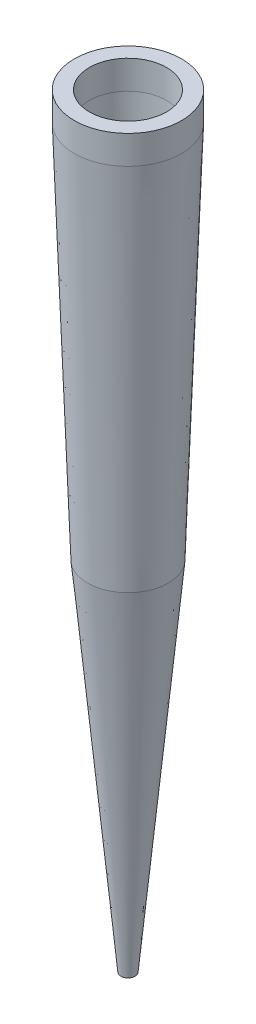
SolidWorks part; units mm, degrees
ref_plane "Ebene vorne" through (0, 0, 0) normal (0, 0, 1) x (1, 0, 0)
ref_plane "Ebene oben" through (0, 0, 0) normal (0, 1, 0) x (1, 0, 0)
ref_plane "Ebene rechts" through (0, 0, 0) normal (1, 0, 0) x (0, 0, -1)
sketch "Skizze1" plane through (0, 0, 0) normal (0, 0, 1) x (1, 0, 0)
  line L0 (0, 0) -> (0, -16.3942) construction
  line L1 (-2.7, 0) -> (-2.7, -2)
  line L2 (-2.7, -2) -> (-1.7746, -28.5)
  line L3 (-1.7746, -28.5) -> (-0.5, -53.5)
  line L5 (-0.5, -53.5) -> (-2.8246, -28.5)
  line L6 (-2.8246, -28.5) -> (-3.75, -2)
  line L7 (-3.75, -2) -> (-3.75, 0)
  line L8 (-3.75, 0) -> (-2.7, 0)
  dimension "D1" = 2.7
  dimension "D2" = 53.5
  dimension "D3" = 2
  dimension "D4" = 7.5
  dimension "D5" = 1
  dimension "D6" = 182
  dimension "D7" = 25
revolve "Rotation1" add sketch "Skizze1" angle 360 about L0
